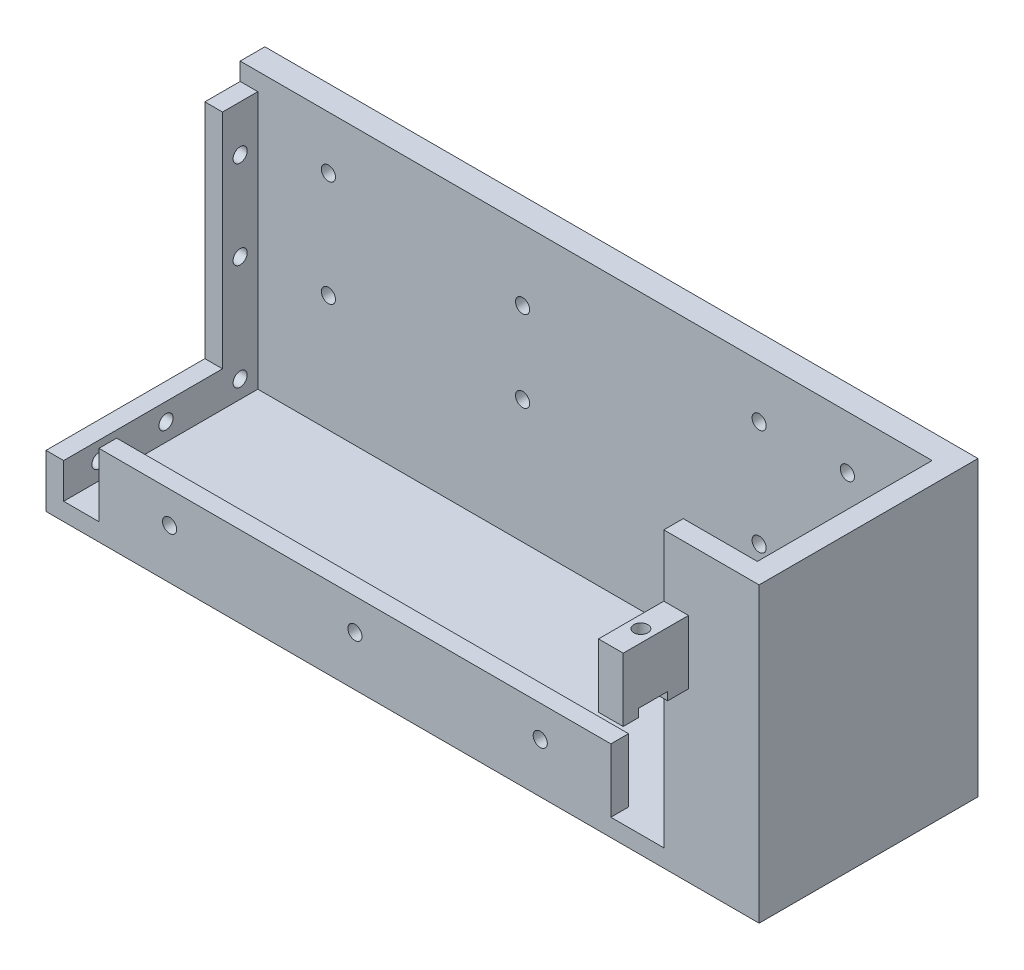
SolidWorks part; units mm, degrees
ref_plane "Front Plane" through (0, 0, 0) normal (0, 0, 1) x (1, 0, 0)
ref_plane "Top Plane" through (0, 0, 0) normal (0, 1, 0) x (1, 0, 0)
ref_plane "Right Plane" through (0, 0, 0) normal (1, 0, 0) x (0, 0, -1)
sketch "Sketch1" plane through (0, 0, 0) normal (0, 1, 0) x (1, 0, 0)
  line L1 (-44.8485, 23.3333) -> (137.1515, 23.3333)
  line L2 (-44.8485, 23.3333) -> (-44.8485, -38.6667)
  line L3 (-44.8485, -38.6667) -> (137.1515, -38.6667)
  line L4 (137.1515, 23.3333) -> (137.1515, -38.6667)
  dimension "D1" = 62
  dimension "D2" = 182
extrude "Boss-Extrude1" add sketch "Sketch1" along normal blind 5
sketch "Sketch2" plane through (0, 5, 0) normal (0, 1, 0) x (1, 0, 0)
  line L0 (-44.8485, -38.6667) -> (137.1515, -38.6667) construction
  line L1 (-22.8485, -38.6667) -> (122.1515, -38.6667)
  line L2 (-22.8485, -38.6667) -> (-22.8485, -33.6667)
  line L3 (-22.8485, -33.6667) -> (122.1515, -33.6667)
  line L4 (122.1515, -38.6667) -> (122.1515, -33.6667)
  line L5 (-44.8485, 23.3333) -> (-44.8485, -38.6667) construction
  line L6 (137.1515, -38.6667) -> (137.1515, 23.3333) construction
  dimension "D1" = 22
  dimension "D2" = 15
  dimension "D3" = 5
extrude "Boss-Extrude2" add sketch "Sketch2" along normal blind 18
sketch "Sketch3" plane through (0, 0, 33.6667) normal (0, 0, -1) x (-1, 0, 0)
  line L0 (-122.1515, 5) -> (22.8485, 5) construction
  line L1 (-122.1515, 23) -> (-122.1515, 5) construction
  line L2 (22.8485, 23) -> (22.8485, 5) construction
  circle A0 centre (-102.1515, 14.1) radius 2
  circle A1 centre (-49.6515, 14.1) radius 2
  circle A2 centre (2.8485, 14.1) radius 2
  dimension "D1" = 9.1
  dimension "D3" = 52.5
  dimension "D5" = 9.1
  dimension "D2" = 20
  dimension "D4" = 20
  dimension "D6" = 52.5
extrude "Cut-Extrude1" cut sketch "Sketch3" against normal blind 18
sketch "Sketch4" plane through (0, 5, 0) normal (0, 1, 0) x (1, 0, 0)
  line L0 (-44.8485, -38.6667) -> (-22.8485, -38.6667) construction
  line L1 (-44.8485, 23.3333) -> (-37.8485, 23.3333)
  line L2 (-44.8485, 23.3333) -> (-44.8485, -38.6667)
  line L3 (-44.8485, -38.6667) -> (-37.8485, -38.6667)
  line L4 (-37.8485, 23.3333) -> (-37.8485, -38.6667)
  dimension "D1" = 7
extrude "Boss-Extrude3" add sketch "Sketch4" along normal blind 78
sketch "Sketch5" plane through (0, 5, 0) normal (0, 1, 0) x (1, 0, 0)
  line L0 (-37.8485, -38.6667) -> (-37.8485, 23.3333) construction
  line L1 (137.1515, 23.3333) -> (-37.8485, 23.3333)
  line L2 (137.1515, 23.3333) -> (137.1515, 16.3333)
  line L3 (137.1515, 16.3333) -> (-37.8485, 16.3333)
  line L4 (-37.8485, 23.3333) -> (-37.8485, 16.3333)
  dimension "D1" = 7
extrude "Boss-Extrude4" add sketch "Sketch5" along normal blind 78
sketch "Sketch6" plane through (0, 0, 38.6667) normal (0, 0, 1) x (1, 0, 0)
  line L0 (-44.8485, 83) -> (-44.8485, 0) construction
  line L1 (-44.8485, 65.5) -> (-37.8485, 65.5)
  line L2 (-44.8485, 65.5) -> (-44.8485, 47.5)
  line L3 (-44.8485, 47.5) -> (-37.8485, 47.5)
  line L4 (-37.8485, 65.5) -> (-37.8485, 47.5)
  line L5 (-37.8485, 83) -> (-37.8485, 5) construction
  line L6 (-44.8485, 83) -> (-37.8485, 83) construction
  dimension "D1" = 17.5
  dimension "D2" = 18
extrude "Boss-Extrude5" add sketch "Sketch6" along normal blind 18.5
sketch "Sketch7" plane through (0, 65.5, 0) normal (0, 1, 0) x (1, 0, 0)
  line L0 (-44.8485, -38.6667) -> (-37.8485, -38.6667) construction
  line L1 (-44.8485, -57.1667) -> (-44.8485, -38.6667) construction
  circle A0 centre (-41.3485, -48.6667) radius 2
  dimension "D1" = 10
  dimension "D2" = 3.5
extrude "Cut-Extrude2" cut sketch "Sketch7" against normal blind 18 contours A0
sketch "Sketch8" plane through (0, 47.5, 0) normal (0, -1, 0) x (1, 0, 0)
  line L0 (-44.8485, 57.1667) -> (-44.8485, 38.6667) construction
  line L1 (-44.8485, 52.7667) -> (-37.8485, 52.7667)
  line L2 (-44.8485, 52.7667) -> (-44.8485, 44.5667)
  line L3 (-44.8485, 44.5667) -> (-37.8485, 44.5667)
  line L4 (-37.8485, 52.7667) -> (-37.8485, 44.5667)
  line L5 (-37.8485, 57.1667) -> (-37.8485, 38.6667) construction
  circle A0 centre (-41.3485, 48.6667) radius 2 construction
  dimension "D1" = 8.2
  dimension "D2" = 4.1
extrude "Cut-Extrude3" cut sketch "Sketch8" against normal blind 2.3
sketch "Sketch9" plane through (0, 0, 33.6667) normal (0, 0, -1) x (-1, 0, 0)
  line L0 (-122.1515, 23) -> (-122.1515, 5) construction
  line L1 (-122.1515, 5) -> (22.8485, 5) construction
  circle A0 centre (-102.1515, 14.1) radius 4.4408
  circle A1 centre (-49.6515, 14.1) radius 4.5
  circle A2 centre (2.8485, 14.1) radius 4.5
  dimension "D1" = 52.5
  dimension "D4" = 9.1
  dimension "D5" = 9.1
  dimension "D2" = 20
  dimension "D3" = 9.1
extrude "Cut-Extrude4" cut sketch "Sketch9" against normal blind 2.2
sketch "Sketch12" plane through (0, 5, 0) normal (0, 1, 0) x (1, 0, 0)
  line L0 (122.1515, -38.6667) -> (137.1515, -38.6667) construction
  line L1 (137.1515, 16.3333) -> (132.1515, 16.3333)
  line L2 (137.1515, 16.3333) -> (137.1515, -38.6667)
  line L3 (137.1515, -38.6667) -> (132.1515, -38.6667)
  line L4 (132.1515, 16.3333) -> (132.1515, -38.6667)
  dimension "D1" = 5
extrude "Boss-Extrude6" add sketch "Sketch12" along normal blind 10
sketch "Sketch13" plane through (0, 15, 0) normal (0, 1, 0) x (1, 0, 0)
  line L0 (132.1515, 16.3333) -> (132.1515, -38.6667) construction
  line L1 (137.1515, 16.3333) -> (132.1515, 16.3333)
  line L2 (137.1515, 16.3333) -> (137.1515, 6.3333)
  line L3 (137.1515, 6.3333) -> (132.1515, 6.3333)
  line L4 (132.1515, 16.3333) -> (132.1515, 6.3333)
  dimension "D1" = 10
extrude "Boss-Extrude7" add sketch "Sketch13" along normal blind 63
sketch "Sketch15" plane through (137.1515, 0, 0) normal (1, 0, 0) x (0, 0, -1)
  line L0 (-38.6667, 15) -> (-38.6667, 0) construction
  line L1 (-38.6667, 0) -> (23.3333, 0) construction
  line L2 (23.3333, 83) -> (23.3333, 0) construction
  circle A0 centre (11.3333, 65) radius 2
  circle A1 centre (11.3333, 40) radius 2
  circle A2 centre (11.3333, 10) radius 2
  circle A3 centre (-28.6667, 10) radius 2
  circle A4 centre (-9.6667, 10) radius 2
  dimension "D1" = 10
  dimension "D2" = 10
  dimension "D3" = 10
  dimension "D4" = 10
  dimension "D5" = 12
  dimension "D6" = 19
  dimension "D7" = 21
  dimension "D8" = 30
  dimension "D9" = 25
  dimension "D10" = 12
  dimension "D11" = 12
extrude "Cut-Extrude6" cut sketch "Sketch15" against normal blind 63
sketch "Sketch16" plane through (-44.8485, 0, 0) normal (-1, 0, 0) x (0, 0, 1)
  line L1 (-23.3333, 83) -> (38.6667, 83)
  line L2 (-23.3333, 83) -> (-23.3333, 0)
  line L3 (-23.3333, 0) -> (38.6667, 0)
  line L4 (38.6667, 83) -> (38.6667, 0)
extrude "Boss-Extrude8" add sketch "Sketch16" along normal blind 20
sketch "Sketch17" plane through (0, 83, 0) normal (0, 1, 0) x (1, 0, 0)
  line L0 (-64.8485, -38.6667) -> (-37.8485, -38.6667) construction
  line L1 (-37.8485, 16.3333) -> (-58.8485, 16.3333)
  line L2 (-37.8485, 16.3333) -> (-37.8485, -33.1667)
  line L3 (-37.8485, -33.1667) -> (-58.8485, -33.1667)
  line L4 (-58.8485, 16.3333) -> (-58.8485, -33.1667)
  line L5 (-64.8485, -38.6667) -> (-64.8485, 23.3333) construction
  dimension "D1" = 5.5
  dimension "D2" = 6
extrude "Cut-Extrude7" cut sketch "Sketch17" against normal blind 78
sketch "Sketch18" plane through (0, 0, -16.3333) normal (0, 0, 1) x (1, 0, 0)
  line L0 (-58.8485, 83) -> (137.1515, 83) construction
  line L1 (-58.8485, 5) -> (-58.8485, 83) construction
  circle A0 centre (-34.8485, 68) radius 2
  circle A1 centre (-9.8485, 68) radius 2
  circle A2 centre (-34.8485, 38) radius 2
  circle A3 centre (-9.8485, 38) radius 2
  dimension "D1" = 15
  dimension "D3" = 25
  dimension "D5" = 15
  dimension "D2" = 24
  dimension "D4" = 30
  dimension "D6" = 30
  dimension "D7" = 25
extrude "Cut-Extrude8" cut sketch "Sketch18" against normal blind 82
sketch "Sketch19" plane through (0, 0, -16.3333) normal (0, 0, 1) x (1, 0, 0)
  line L0 (-64.8485, 0) -> (-64.8485, 83) construction
  line L1 (-58.8485, 83) -> (137.1515, 83) construction
  circle A0 centre (57.1515, 63) radius 2
  circle A1 centre (57.1515, 40) radius 2
  dimension "D1" = 122
  dimension "D2" = 122
  dimension "D3" = 23
  dimension "D4" = 20
extrude "Cut-Extrude9" cut sketch "Sketch19" against normal blind 82
sketch "Sketch21" plane through (0, 0, -23.3333) normal (0, 0, -1) x (-1, 0, 0)
  line L0 (-137.1515, 83) -> (64.8485, 83) construction
  line L1 (-137.1515, 83) -> (-137.1515, 0) construction
  circle A0 centre (-112.1515, 38) radius 2
  circle A1 centre (-112.1515, 68) radius 2
  dimension "D1" = 15
  dimension "D2" = 30
  dimension "D3" = 25
extrude "Cut-Extrude10" cut sketch "Sketch21" against normal blind 10
mirror "Mirror1" about plane through (-64.8485, 0, 0) normal (-1, 0, 0) of bodies 118
delete or keep bodies "Body-Delete/Keep 1" type delete bodies bodies 118
